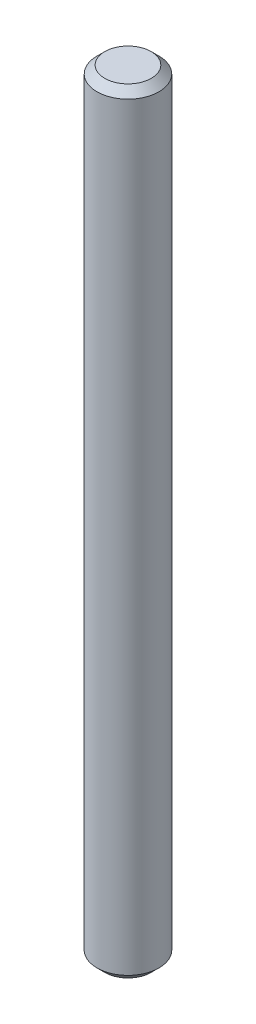
SolidWorks part; units mm, degrees
ref_plane "Front Plane" through (0, 0, 0) normal (0, 0, 1) x (1, 0, 0)
ref_plane "Top Plane" through (0, 0, 0) normal (0, 1, 0) x (1, 0, 0)
ref_plane "Right Plane" through (0, 0, 0) normal (1, 0, 0) x (0, 0, -1)
sketch "Sketch1" plane through (0, 0, 0) normal (0, 1, 0) x (1, 0, 0)
  circle A0 centre (0, 0) radius 2
  dimension "D1" = 4
extrude "Boss-Extrude1" add sketch "Sketch1" along normal blind 50
chamfer "Chamfer1" distance 0.5 angle 45 2 edges at (0, 0, 2) (0, 50, 2)
